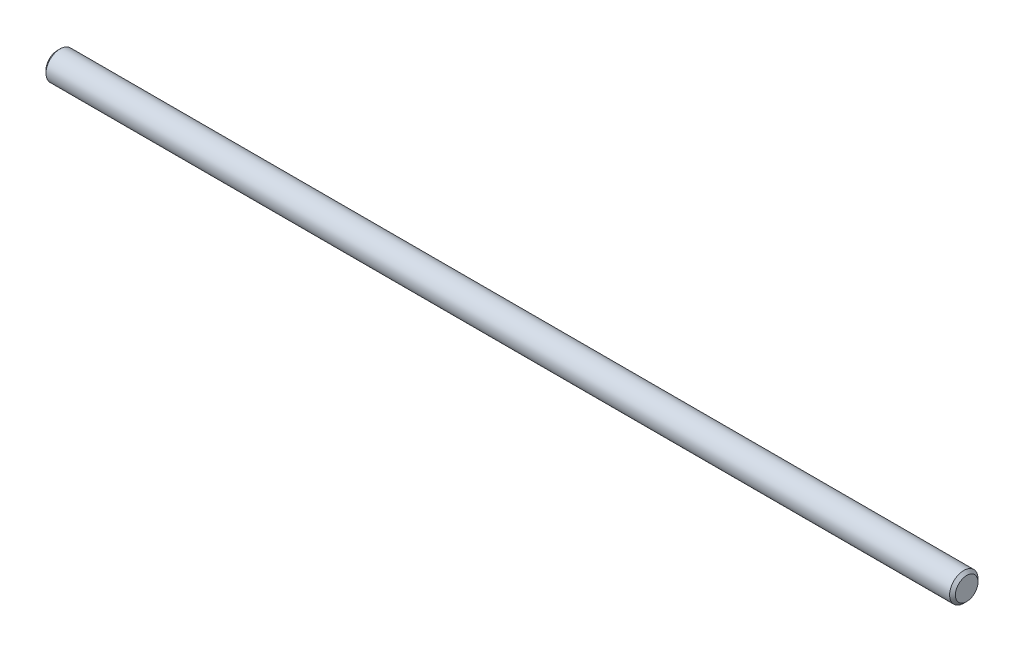
SolidWorks part; units mm, degrees
material "AISI 304"
ref_plane "正面" through (0, 0, 0) normal (0, 0, 1) x (1, 0, 0)
ref_plane "平面" through (0, 0, 0) normal (0, 1, 0) x (1, 0, 0)
ref_plane "右側面" through (0, 0, 0) normal (1, 0, 0) x (0, 0, -1)
ref_plane "Plane1" through (0, 0, 0) normal (0, 0, 1) x (1, 0, 0)
sketch "Sketch1" plane through (0, 0, 0) normal (0, 0, 1) x (1, 0, 0)
  line L0 (-48, 0) -> (-48, 1.1935)
  line L1 (-48, 1.1935) -> (-47.6935, 1.5)
  line L2 (-47.6935, 1.5) -> (47.6935, 1.5)
  line L3 (47.6935, 1.5) -> (48, 1.1935)
  line L4 (48, 1.1935) -> (48, 0)
  line L5 (48, 0) -> (-48, 0)
  line L6 (48, 0) -> (-48, 0) construction
  dimension "D1" = 1.5
revolve "Revolve1" add sketch "Sketch1" angle 360 about L6
cosmetic thread "Cosmetic Thread1" parameters "D1"=96, "D2"=2.387
